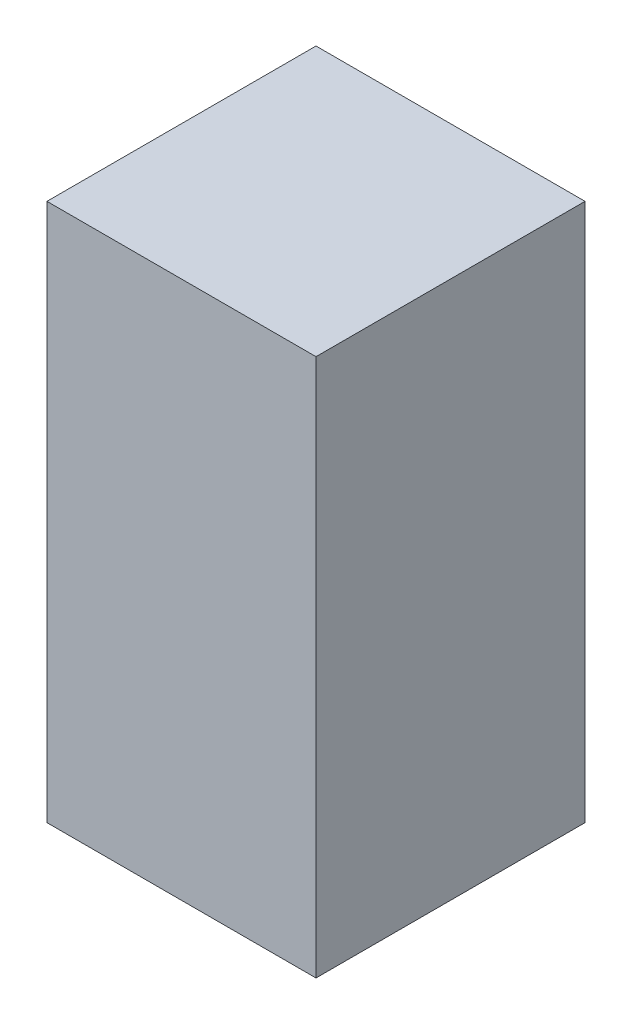
SolidWorks part; units mm, degrees
ref_plane "Top Plane" through (0, 0, 0) normal (0, 0, 1) x (1, 0, 0)
ref_plane "Front Plane" through (0, 0, 0) normal (0, 1, 0) x (1, 0, 0)
ref_plane "Right Plane" through (0, 0, 0) normal (1, 0, 0) x (0, 0, -1)
sketch "Sketch1" plane through (0, 0, 0) normal (0, 1, 0) x (1, 0, 0)
  line L1 (0, 0) -> (50, 0)
  line L2 (0, 0) -> (0, 50)
  line L3 (0, 50) -> (50, 50)
  line L4 (50, 0) -> (50, 50)
  dimension "D1" = 50
  dimension "D2" = 50
extrude "Boss-Extrude1" add sketch "Sketch1" along normal blind 100 contours L3 L4 L1 L2
